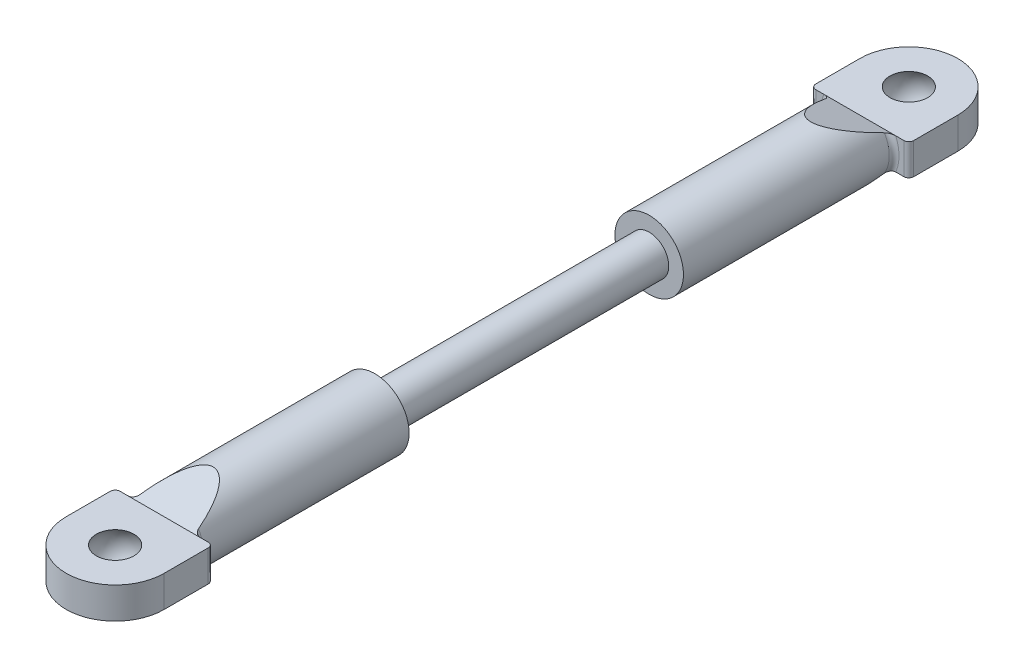
SolidWorks part; units mm, degrees
ref_plane "Front Plane" through (0, 0, 0) normal (0, 0, 1) x (1, 0, 0)
ref_plane "Top Plane" through (0, 0, 0) normal (0, 1, 0) x (1, 0, 0)
ref_plane "Right Plane" through (0, 0, 0) normal (1, 0, 0) x (0, 0, -1)
sketch "Sketch1" plane through (0, 0, 0) normal (0, 0, 1) x (1, 0, 0)
  circle A0 centre (0, 0) radius 2
  dimension "D1" = 4
extrude "Screw Section" add sketch "Sketch1" along normal blind 14 contours A0
sketch "Sketch2" plane through (0, 0, 14) normal (0, 0, 1) x (1, 0, 0)
  circle A0 centre (0, 0) radius 3.5
  dimension "D1" = 7
extrude "Bar Section" add sketch "Sketch2" along normal blind 21.5
sketch "Sketch3" plane through (0, 0, 0) normal (0, 1, 0) x (1, 0, 0)
  line L0 (5, -35.5) -> (-5, -35.5)
  line L1 (-5, -35.5) -> (-5, -40.5)
  line L2 (5, -35.5) -> (5, -40.5)
  line L3 (-3.5, -35.5) -> (3.5, -35.5) construction
  arc A0 (-5, -40.5) -> (5, -40.5) centre (0, -40.5) ccw
  point P4 (0, -45.5)
  dimension "D1" = 5
  dimension "D2" = 10
  dimension "D3" = 10
extrude "Mount Section" add sketch "Sketch3" along normal mid plane 3.2
sketch "Sketch4" plane through (0, 0, 0) normal (1, 0, 0) x (0, 0, -1)
  line L0 (-30.5, -3.5) -> (-35.5, -1.6)
  line L1 (-35.5, -3.5) -> (-14, -3.5) construction
  line L2 (-35.5, -1.6) -> (-35.5, -3.5)
  line L3 (-35.5, -1.6) -> (-35.5, -3.5) construction
  line L4 (-35.5, -3.5) -> (-30.5, -3.5)
  line L5 (-30.5, 3.5) -> (-35.5, 1.6)
  line L6 (-35.5, 3.5) -> (-35.5, 1.6) construction
  line L7 (-35.5, 3.5) -> (-30.5, 3.5)
  line L9 (-35.5, 1.6) -> (-35.5, 3.5)
  dimension "D1" = 5
  dimension "D2" = 1.9
extrude "Bar Taper" cut sketch "Sketch4" against normal through all both and the other way through all
fillet "Mount Fillet" radius 0.5 4 edges at (-5, 0, 35.5) (3.5, 0, 35.5) (-3.5, 0, 35.5) (5, 0, 35.5)
sketch "Sketch6" plane through (0, 0, 0) normal (1, 0, 0) x (0, 0, -1)
  line L0 (-40.5, 1.6) -> (-40.5, -1.6) construction
  line L1 (-45.5, -1.6) -> (-40.5, -1.6) construction
  line L2 (-40.5, 1.6) -> (-45.5, 1.6) construction
  line L4 (-42.4209, -1.6) -> (-40.5, -1.6)
  line L5 (-40.5, -1.6) -> (-40.5, 1.6)
  line L6 (-40.5, 1.6) -> (-42.4209, 1.6)
  arc A0 (-42.4209, -1.6) -> (-42.4209, 1.6) centre (-40.5, 0) cw
  dimension "D1" = 2.5
revolve "Ball Hole" cut sketch "Sketch6" angle 360 about L5
mirror "Mirror" of "Ball Hole", "Bar Section", "Bar Taper", "Mount Section", "Mount Fillet", "Screw Section"
ref_point "Point1"
ref_point "Point2"
